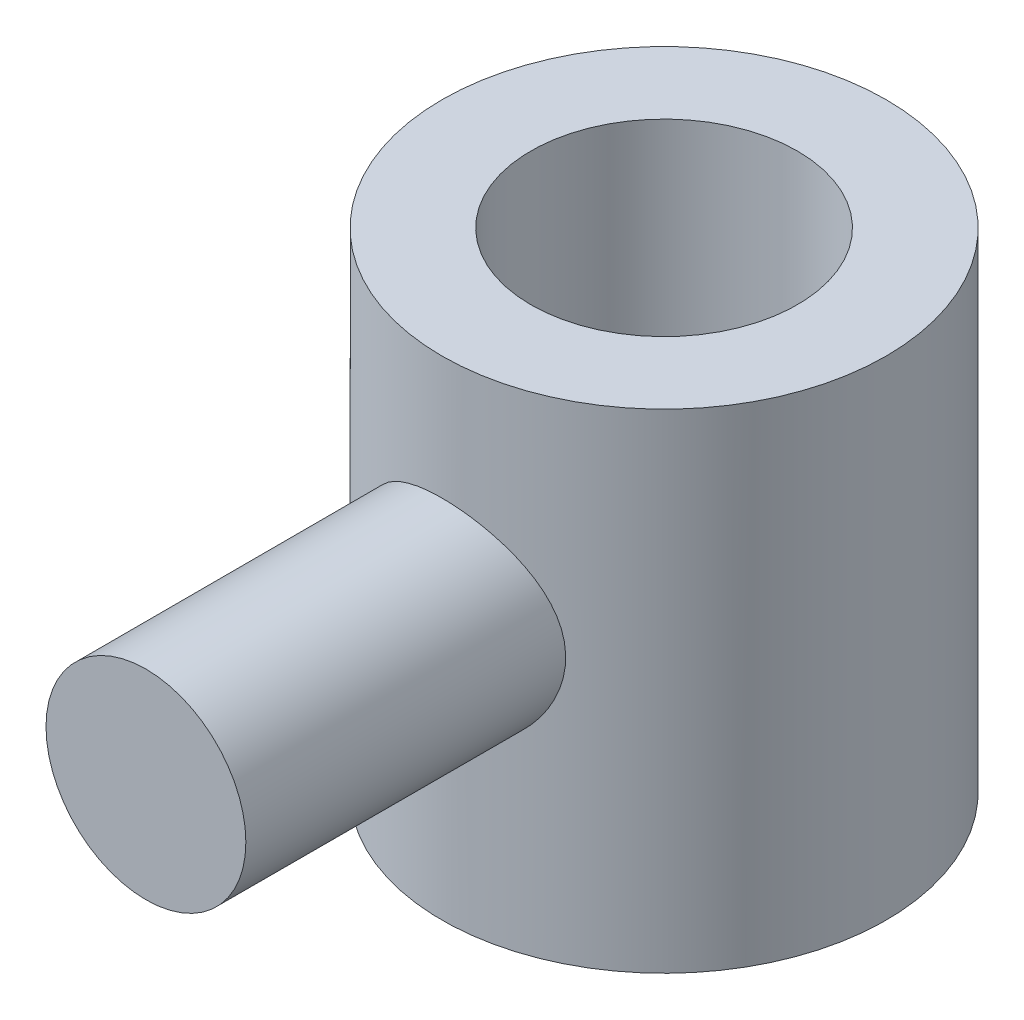
SolidWorks part; units mm, degrees
material "Ti-6Al-2Sn-2Zr-2Mo-2Cr-0.25Si (SS)"
ref_plane "Front Plane" through (0, 0, 0) normal (0, 0, 1) x (1, 0, 0)
ref_plane "Top Plane" through (0, 0, 0) normal (0, 1, 0) x (1, 0, 0)
ref_plane "Right Plane" through (0, 0, 0) normal (1, 0, 0) x (0, 0, -1)
sketch "Sketch1" plane through (0, 0, 0) normal (0, 1, 0) x (1, 0, 0)
  circle A0 centre (0, 0) radius 150
  dimension "D1" = 300
extrude "Boss-Extrude1" add sketch "Sketch1" along normal blind 500
sketch "Sketch2" plane through (0, 0, 0) normal (0, -1, 0) x (1, 0, 0)
  circle A0 centre (0, 0) radius 90
  circle A1 centre (0, 0) radius 150 construction
  circle A2 centre (0, 0) radius 150
  dimension "D1" = 60
extrude "Cut-Extrude1" cut sketch "Sketch2" against normal blind 70
sketch "Sketch4" plane through (0, 0, 0) normal (0, 0, 1) x (1, 0, 0)
  line L0 (0, 0) -> (0, 498.8605) construction
  circle A0 centre (0, 249.4303) radius 67.5
  dimension "D1" = 135
extrude "Boss-Extrude2" add sketch "Sketch4" along normal blind 350
sketch "Sketch5" plane through (0, 500, 0) normal (0, 1, 0) x (1, 0, 0)
  circle A0 centre (0, 0) radius 150
extrude "Cut-Extrude3" cut sketch "Sketch5" against normal blind 100
sketch "Sketch6" plane through (0, 0, 0) normal (0, -1, 0) x (1, 0, 0)
  circle A0 centre (0, 0) radius 90
extrude "Cut-Extrude4" cut sketch "Sketch6" against normal through all
